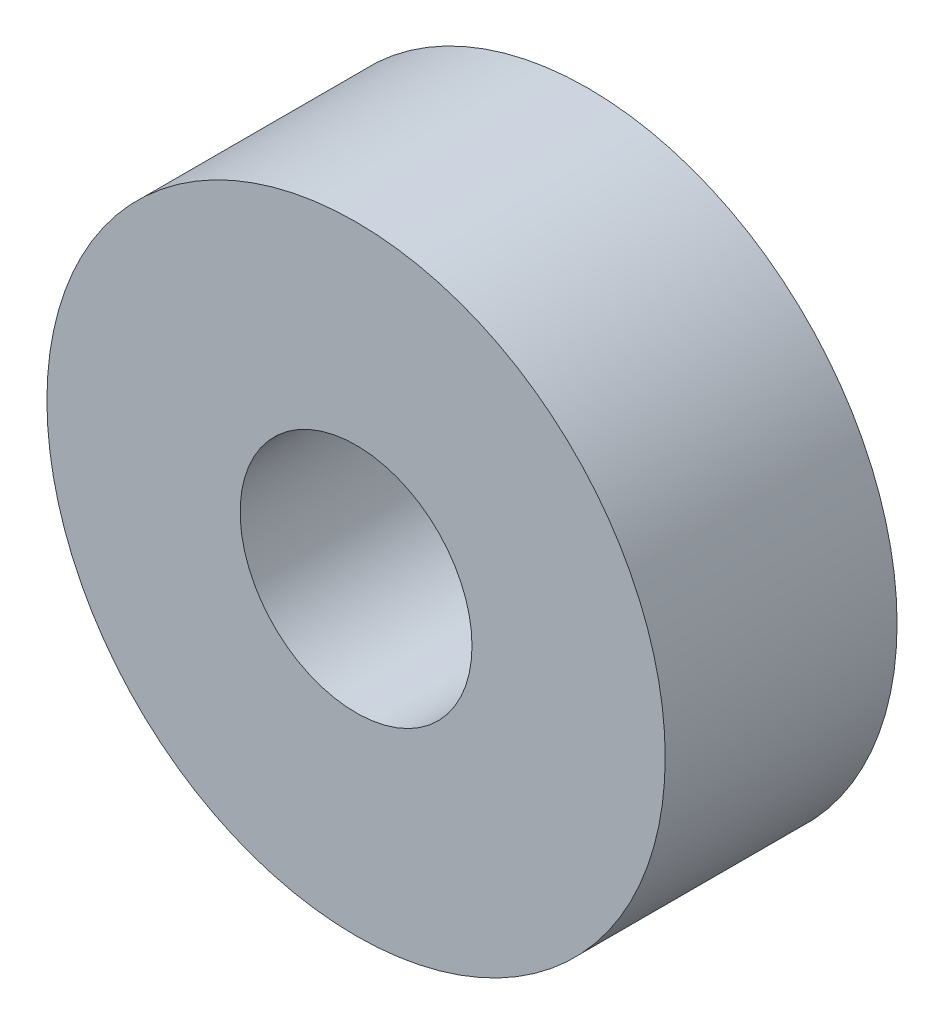
SolidWorks part; units mm, degrees
ref_plane "Front Plane" through (0, 0, 0) normal (0, 0, 1) x (1, 0, 0)
ref_plane "Top Plane" through (0, 0, 0) normal (0, 1, 0) x (1, 0, 0)
ref_plane "Right Plane" through (0, 0, 0) normal (1, 0, 0) x (0, 0, -1)
sketch "Sketch1" plane through (0, 0, 0) normal (0, 0, 1) x (1, 0, 0)
  circle A0 centre (0, 0) radius 16
  circle A1 centre (0, 0) radius 6
  dimension "D1" = 32
  dimension "D2" = 12
extrude "Boss-Extrude1" add sketch "Sketch1" along normal blind 12
